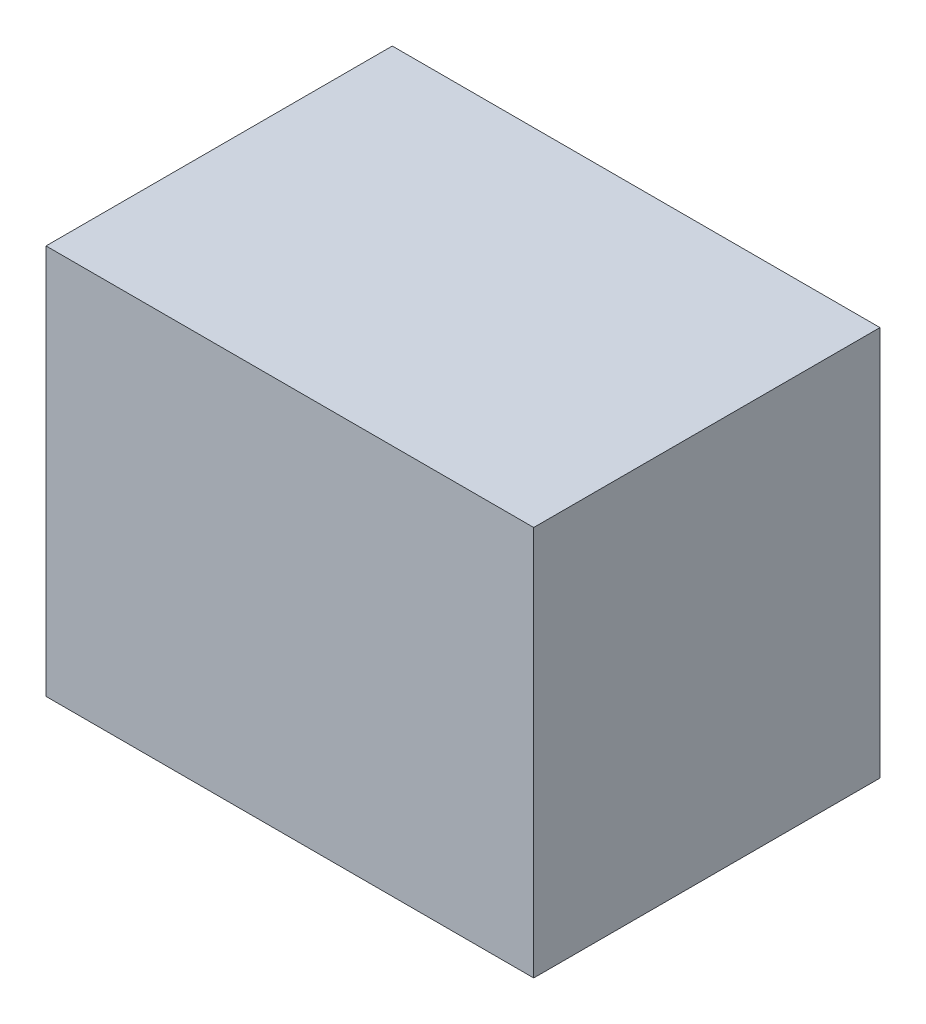
SolidWorks part; units mm, degrees
ref_plane "Front Plane" through (0, 0, 0) normal (0, 0, 1) x (1, 0, 0)
ref_plane "Top Plane" through (0, 0, 0) normal (0, 1, 0) x (1, 0, 0)
ref_plane "Right Plane" through (0, 0, 0) normal (1, 0, 0) x (0, 0, -1)
sketch "Sketch1" plane through (0, 0, 0) normal (0, 0, 1) x (1, 0, 0)
  line L0 (-17.8, 38.6) -> (17.8, 38.6) construction
  line L1 (11.5, 38.6) -> (-38.5, 38.6)
  line L2 (11.5, 38.6) -> (11.5, 78.6)
  line L3 (11.5, 78.6) -> (-38.5, 78.6)
  line L4 (-38.5, 38.6) -> (-38.5, 78.6)
  line L5 (17.8, 38.6) -> (17.8, -12) construction
  dimension "D1" = 6.3
  dimension "D2" = 40
  dimension "D3" = 50
extrude "Boss-Extrude1" add sketch "Sketch1" against normal up to surface (35.5 mm away)
